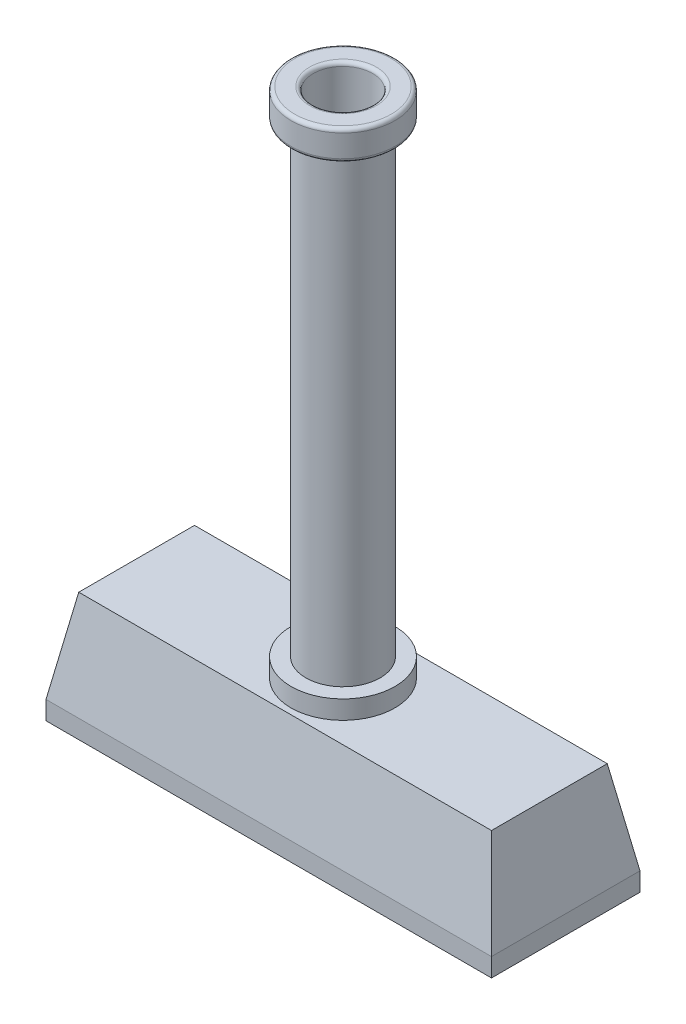
SolidWorks part; units mm, degrees
ref_plane "Front Plane" through (0, 0, 0) normal (0, 0, 1) x (1, 0, 0)
ref_plane "Top Plane" through (0, 0, 0) normal (0, 1, 0) x (1, 0, 0)
ref_plane "Right Plane" through (0, 0, 0) normal (1, 0, 0) x (0, 0, -1)
sketch "Sketch1" plane through (0, 0, 0) normal (0, 1, 0) x (1, 0, 0)
  line L1 (-60, 20) -> (60, 20)
  line L2 (-60, 20) -> (-60, -20)
  line L3 (-60, -20) -> (60, -20)
  line L4 (60, 20) -> (60, -20)
  line L5 (-60, 20) -> (60, -20) construction
  line L6 (-60, -20) -> (60, 20) construction
  point P0 (0, 0)
  dimension "D1" = 40
  dimension "D2" = 120
extrude "Boss-Extrude1" add sketch "Sketch1" along normal blind 25 draft 10
sketch "Sketch2" plane through (0, 25, 0) normal (0, 1, 0) x (1, 0, 0)
  circle A0 centre (0, 0) radius 14
extrude "Boss-Extrude2" add sketch "Sketch2" along normal blind 5
sketch "Sketch3" plane through (0, 30, 0) normal (0, 1, 0) x (1, 0, 0)
  circle A0 centre (0, 0) radius 10
extrude "Boss-Extrude3" add sketch "Sketch3" along normal blind 125
sketch "Sketch4" plane through (0, 155, 0) normal (0, 1, 0) x (1, 0, 0)
  circle A0 centre (0, 0) radius 14
extrude "Boss-Extrude4" add sketch "Sketch4" along normal blind 8
sketch "Sketch5" plane through (0, 163, 0) normal (0, 1, 0) x (1, 0, 0)
  circle A0 centre (0, 0) radius 8
extrude "Cut-Extrude1" cut sketch "Sketch5" against normal blind 150
fillet "Fillet1" radius 1 4 edges at (0, 163, 8) (0, 155, 14) (0, 163, 14) (0, 155, 10)
sketch "Sketch6" plane through (0, 0, 0) normal (0, -1, 0) x (1, 0, 0)
  line L1 (-60, 20) -> (60, 20)
  line L2 (-60, 20) -> (-60, -20)
  line L3 (-60, -20) -> (60, -20)
  line L4 (60, 20) -> (60, -20)
  line L5 (-60, 20) -> (60, -20) construction
  line L6 (-60, -20) -> (60, 20) construction
  point P0 (0, 0)
extrude "Boss-Extrude5" add sketch "Sketch6" along normal blind 5
